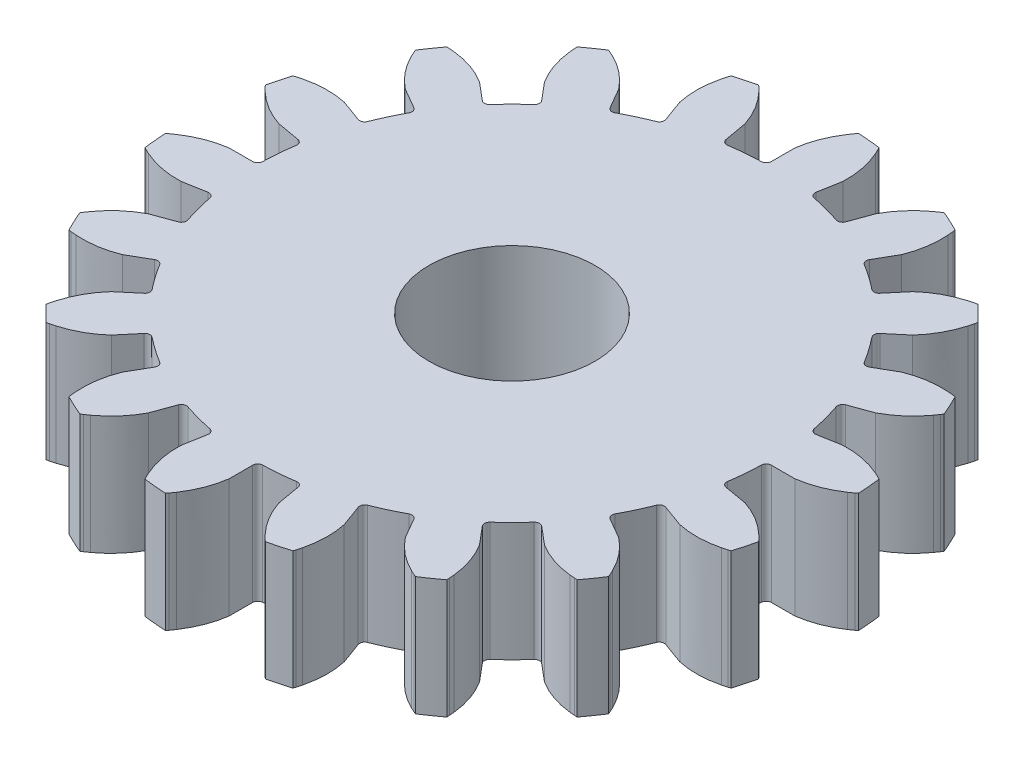
SolidWorks part; units mm, degrees
ref_plane "Front Plane" through (0, 0, 0) normal (0, 0, 1) x (1, 0, 0)
ref_plane "Top Plane" through (0, 0, 0) normal (0, 1, 0) x (1, 0, 0)
ref_plane "Right Plane" through (0, 0, 0) normal (1, 0, 0) x (0, 0, -1)
sketch "Sketch1" plane through (0, 0, 0) normal (0, 1, 0) x (1, 0, 0)
  line L0 (-10.9424, 9.3007) -> (-10.0385, 8.5423)
  line L1 (-8.5423, 10.0385) -> (-9.3007, 10.9424)
  line L2 (-7.1014, 12.4823) -> (-6.5115, 11.4605)
  line L3 (-2.4039, 14.1584) -> (-2.1991, 12.9964)
  line L4 (-0.0911, 13.1808) -> (-0.0911, 14.3607)
  line L5 (2.5835, 14.1267) -> (2.3786, 12.9647)
  line L6 (11.0595, 9.1611) -> (10.1557, 8.4026)
  line L7 (12.9964, -2.1991) -> (14.1584, -2.404)
  line L8 (13.4635, -4.9973) -> (12.3547, -4.5938)
  line L9 (4.5938, -12.3547) -> (4.9973, -13.4635)
  line L10 (-4.4225, -12.4171) -> (-4.826, -13.5258)
  line L11 (-8.4026, -10.1557) -> (-9.1611, -11.0595)
  line L12 (-12.9647, -2.3786) -> (-14.1267, -2.5835)
  line L13 (-14.3607, 0.0912) -> (-13.1808, 0.0912)
  line L14 (-12.9964, 2.1991) -> (-14.1584, 2.404)
  line L15 (-13.4635, 4.9973) -> (-12.3547, 4.5938)
  line L16 (-11.4605, 6.5115) -> (-12.4823, 7.1014)
  line L17 (2.4039, -14.1584) -> (2.1991, -12.9964)
  line L18 (-11.3693, -6.6693) -> (-12.3912, -7.2593)
  line L19 (8.4026, 10.1557) -> (9.1611, 11.0595)
  line L20 (-4.5938, 12.3547) -> (-4.9973, 13.4635)
  line L21 (-13.5258, -4.826) -> (-12.4171, -4.4224)
  line L22 (-2.5835, -14.1267) -> (-2.3786, -12.9647)
  line L23 (13.5258, 4.826) -> (12.4171, 4.4224)
  line L24 (-7.2593, -12.3912) -> (-6.6693, -11.3693)
  line L25 (12.9647, 2.3786) -> (14.1267, 2.5835)
  line L26 (14.3607, -0.0912) -> (13.1808, -0.0912)
  line L27 (-11.0595, -9.1611) -> (-10.1557, -8.4026)
  line L28 (7.2593, 12.3912) -> (6.6693, 11.3693)
  line L29 (8.5423, -10.0385) -> (9.3007, -10.9424)
  line L30 (10.9424, -9.3007) -> (10.0385, -8.5423)
  line L31 (11.4605, -6.5115) -> (12.4823, -7.1014)
  line L32 (11.3693, 6.6693) -> (12.3912, 7.2593)
  line L33 (7.1014, -12.4823) -> (6.5115, -11.4605)
  line L34 (4.4225, 12.4171) -> (4.826, 13.5258)
  line L35 (0.0911, -13.1808) -> (0.0911, -14.3607)
  circle A0 centre (0, 0) radius 4.191
  arc A2 (13.2871, -9.9977) -> (13.9392, -9.0664) centre (0, 0) ccw
  arc A4 (-15.3018, -6.5081) -> (-14.8213, -7.5385) centre (0, 0) ccw
  arc A6 (15.3018, 6.5081) -> (14.8213, 7.5385) centre (0, 0) ccw
  arc A8 (-13.2871, 9.9977) -> (-13.9392, 9.0664) centre (0, 0) ccw
  arc A10 (3.7521, -16.1994) -> (4.8503, -15.9052) centre (0, 0) ccw
  arc A12 (-9.0664, 13.9392) -> (-9.9977, 13.2871) centre (0, 0) ccw
  arc A14 (2.0147, 16.5058) -> (0.8821, 16.6049) centre (0, 0) ccw
  arc A16 (-2.0147, -16.5058) -> (-0.8821, -16.6049) centre (0, 0) ccw
  arc A19 (-15.9052, 4.8503) -> (-16.1994, 3.7521) centre (0, 0) ccw
  arc A20 (15.9052, -4.8503) -> (16.1994, -3.7521) centre (0, 0) ccw
  arc A22 (-16.6049, -0.8821) -> (-16.5058, -2.0147) centre (0, 0) ccw
  arc A24 (-7.5385, -14.8213) -> (-6.5081, -15.3018) centre (0, 0) ccw
  arc A26 (7.5385, 14.8213) -> (6.5081, 15.3018) centre (0, 0) ccw
  arc A28 (9.0664, -13.9392) -> (9.9977, -13.2871) centre (0, 0) ccw
  arc A30 (-3.7521, 16.1994) -> (-4.8503, 15.9052) centre (0, 0) ccw
  arc A32 (-12.153, -11.3492) -> (-11.3492, -12.153) centre (0, 0) ccw
  arc A34 (12.153, 11.3492) -> (11.3492, 12.153) centre (0, 0) ccw
  arc A36 (16.6049, 0.8821) -> (16.5058, 2.0147) centre (0, 0) ccw
  arc A38 (-10.0385, 8.5423) -> (-9.6782, 8.569) centre (-9.8721, 8.7406) ccw
  arc A39 (-8.569, 9.6782) -> (-9.6782, 8.569) centre (0, 0) ccw
  arc A40 (-8.569, 9.6782) -> (-8.5423, 10.0385) centre (-8.7406, 9.8721) ccw
  arc A41 (-6.5115, 11.4605) -> (-6.1638, 11.3624) centre (-6.2873, 11.5899) ccw
  arc A42 (-4.7421, 12.0253) -> (-6.1638, 11.3624) centre (0, 0) ccw
  arc A43 (-4.7421, 12.0253) -> (-4.5938, 12.3547) centre (-4.837, 12.2662) ccw
  arc A44 (-2.1991, 12.9964) -> (-1.9059, 12.7853) centre (-1.9441, 13.0413) ccw
  arc A45 (-0.3432, 12.922) -> (-1.9059, 12.7853) centre (0, 0) ccw
  arc A46 (-0.3432, 12.922) -> (-0.0911, 13.1808) centre (-0.35, 13.1808) ccw
  arc A47 (2.3786, 12.9647) -> (2.5818, 12.6661) centre (2.6336, 12.9198) ccw
  arc A48 (4.0971, 12.2601) -> (2.5818, 12.6661) centre (0, 0) ccw
  arc A49 (4.0971, 12.2601) -> (4.4225, 12.4171) centre (4.1792, 12.5056) ccw
  arc A50 (11.0192, 6.7582) -> (11.3693, 6.6693) centre (11.2399, 6.8935) ccw
  arc A51 (12.4171, 4.4224) -> (12.2601, 4.0971) centre (12.5056, 4.1792) ccw
  arc A52 (12.6661, 2.5818) -> (12.2601, 4.0971) centre (0, 0) ccw
  arc A53 (12.6661, 2.5818) -> (12.9647, 2.3786) centre (12.9198, 2.6335) ccw
  arc A54 (12.7853, -1.9059) -> (12.9964, -2.1991) centre (13.0413, -1.9441) ccw
  arc A55 (11.3624, -6.1638) -> (11.4605, -6.5115) centre (11.5899, -6.2873) ccw
  arc A56 (10.0385, -8.5423) -> (9.6782, -8.569) centre (9.8721, -8.7406) ccw
  arc A57 (8.569, -9.6782) -> (9.6782, -8.569) centre (0, 0) ccw
  arc A58 (8.569, -9.6782) -> (8.5423, -10.0385) centre (8.7406, -9.8721) ccw
  arc A59 (-8.0432, -10.1194) -> (-8.4026, -10.1557) centre (-8.2043, -10.3221) ccw
  arc A60 (-10.1557, -8.4026) -> (-10.1194, -8.0432) centre (-10.3221, -8.2043) ccw
  arc A61 (-12.7853, 1.9059) -> (-12.922, 0.3432) centre (0, 0) ccw
  arc A62 (-12.3547, 4.5938) -> (-12.0253, 4.7421) centre (-12.2662, 4.837) ccw
  arc A63 (-11.3624, 6.1638) -> (-12.0253, 4.7421) centre (0, 0) ccw
  arc A64 (-11.3624, 6.1638) -> (-11.4605, 6.5115) centre (-11.5899, 6.2873) ccw
  arc A65 (0.3432, -12.922) -> (0.0911, -13.1808) centre (0.35, -13.1808) ccw
  arc A66 (-2.3786, -12.9647) -> (-2.5818, -12.6661) centre (-2.6336, -12.9198) ccw
  arc A67 (-12.6661, -2.5818) -> (-12.9647, -2.3786) centre (-12.9198, -2.6335) ccw
  arc A68 (-4.0971, -12.2601) -> (-2.5818, -12.6661) centre (0, 0) ccw
  arc A69 (-4.0971, -12.2601) -> (-4.4225, -12.4171) centre (-4.1792, -12.5056) ccw
  arc A70 (-13.1808, 0.0912) -> (-12.922, 0.3432) centre (-13.1808, 0.35) ccw
  arc A71 (-6.6693, -11.3693) -> (-6.7582, -11.0192) centre (-6.8936, -11.2399) ccw
  arc A72 (0.3432, -12.922) -> (1.9059, -12.7853) centre (0, 0) ccw
  arc A73 (-8.0432, -10.1194) -> (-6.7582, -11.0192) centre (0, 0) ccw
  arc A74 (13.1808, -0.0912) -> (12.922, -0.3432) centre (13.1808, -0.35) ccw
  arc A75 (4.7421, -12.0253) -> (4.5938, -12.3547) centre (4.837, -12.2662) ccw
  arc A76 (-11.0192, -6.7582) -> (-10.1194, -8.0432) centre (0, 0) ccw
  arc A77 (-11.0192, -6.7582) -> (-11.3693, -6.6693) centre (-11.2399, -6.8935) ccw
  arc A78 (12.3547, -4.5938) -> (12.0253, -4.7421) centre (12.2662, -4.837) ccw
  arc A79 (-12.4171, -4.4224) -> (-12.2601, -4.0971) centre (-12.5056, -4.1792) ccw
  arc A80 (10.1557, 8.4026) -> (10.1194, 8.0432) centre (10.3221, 8.2043) ccw
  arc A81 (11.3624, -6.1638) -> (12.0253, -4.7421) centre (0, 0) ccw
  arc A82 (-12.6661, -2.5818) -> (-12.2601, -4.0971) centre (0, 0) ccw
  arc A83 (11.0192, 6.7582) -> (10.1194, 8.0432) centre (0, 0) ccw
  arc A84 (4.7421, -12.0253) -> (6.1638, -11.3624) centre (0, 0) ccw
  arc A85 (12.7853, -1.9059) -> (12.922, -0.3432) centre (0, 0) ccw
  arc A86 (-12.7853, 1.9059) -> (-12.9964, 2.1991) centre (-13.0413, 1.9441) ccw
  arc A87 (8.0432, 10.1194) -> (6.7582, 11.0192) centre (0, 0) ccw
  arc A88 (8.0432, 10.1194) -> (8.4026, 10.1557) centre (8.2043, 10.3221) ccw
  arc A89 (6.5115, -11.4605) -> (6.1638, -11.3624) centre (6.2873, -11.5899) ccw
  arc A90 (6.6693, 11.3693) -> (6.7582, 11.0192) centre (6.8936, 11.2399) ccw
  arc A91 (2.1991, -12.9964) -> (1.9059, -12.7853) centre (1.9441, -13.0413) ccw
  spline S0 degree 2 poles (13.2871, -9.9977) (13.2331, -9.9962) (13.1569, -9.9919) knots 0 0 0 0.5 0.5 0.5
  spline S1 degree 3 poles (13.1569, -9.9919) (13.0806, -9.9876) (12.9857, -9.9804) (12.8899, -9.97) knots 0.5 0.5 0.5 0.5 1 1 1 1
  spline S2 degree 3 poles (13.7773, -8.7026) (13.8199, -8.7893) (13.8591, -8.8757) (13.889, -8.9455) knots 0 0 0 0 0.5 0.5 0.5 0.5
  spline S3 degree 2 poles (13.889, -8.9455) (13.919, -9.0153) (13.9392, -9.0664) knots 0.5 0.5 0.5 1 1 1
  spline S4 degree 2 poles (-15.3018, -6.5081) (-15.2735, -6.4621) (-15.2317, -6.3982) knots 0 0 0 0.5 0.5 0.5
  spline S5 degree 3 poles (-15.2317, -6.3982) (-15.1898, -6.3343) (-15.1361, -6.2558) (-15.0792, -6.178) knots 0.5 0.5 0.5 0.5 1 1 1 1
  spline S6 degree 3 poles (-14.4254, -7.5802) (-14.5217, -7.5738) (-14.6161, -7.5645) (-14.6915, -7.5555) knots 0 0 0 0 0.5 0.5 0.5 0.5
  spline S7 degree 2 poles (-14.6915, -7.5555) (-14.7669, -7.5466) (-14.8213, -7.5385) knots 0.5 0.5 0.5 1 1 1
  spline S8 degree 2 poles (15.3018, 6.5081) (15.2735, 6.4621) (15.2317, 6.3982) knots 0 0 0 0.5 0.5 0.5
  spline S9 degree 3 poles (15.2317, 6.3982) (15.1898, 6.3343) (15.1361, 6.2558) (15.0792, 6.178) knots 0.5 0.5 0.5 0.5 1 1 1 1
  spline S10 degree 3 poles (14.4254, 7.5802) (14.5217, 7.5738) (14.6161, 7.5645) (14.6915, 7.5555) knots 0 0 0 0 0.5 0.5 0.5 0.5
  spline S11 degree 2 poles (14.6915, 7.5555) (14.7669, 7.5466) (14.8213, 7.5385) knots 0.5 0.5 0.5 1 1 1
  spline S12 degree 2 poles (-13.2871, 9.9977) (-13.2331, 9.9962) (-13.1569, 9.9919) knots 0 0 0 0.5 0.5 0.5
  spline S13 degree 3 poles (-13.1569, 9.9919) (-13.0806, 9.9876) (-12.9857, 9.9804) (-12.8899, 9.97) knots 0.5 0.5 0.5 0.5 1 1 1 1
  spline S14 degree 3 poles (-13.7773, 8.7026) (-13.8199, 8.7893) (-13.8591, 8.8757) (-13.889, 8.9455) knots 0 0 0 0 0.5 0.5 0.5 0.5
  spline S15 degree 2 poles (-13.889, 8.9455) (-13.919, 9.0153) (-13.9392, 9.0664) knots 0.5 0.5 0.5 1 1 1
  spline S16 degree 2 poles (3.7521, -16.1994) (3.7117, -16.1636) (3.6561, -16.1113) knots 0 0 0 0.5 0.5 0.5
  spline S17 degree 3 poles (3.6561, -16.1113) (3.6004, -16.059) (3.5324, -15.9925) (3.4657, -15.9229) knots 0.5 0.5 0.5 0.5 1 1 1 1
  spline S18 degree 3 poles (4.9601, -15.5225) (4.9371, -15.6162) (4.9115, -15.7076) (4.8896, -15.7803) knots 0 0 0 0 0.5 0.5 0.5 0.5
  spline S19 degree 2 poles (4.8896, -15.7803) (4.8677, -15.853) (4.8503, -15.9052) knots 0.5 0.5 0.5 1 1 1
  spline S20 degree 2 poles (-9.0664, 13.9392) (-9.0162, 13.9194) (-8.946, 13.8892) knots 0 0 0 0.5 0.5 0.5
  spline S21 degree 3 poles (-8.946, 13.8892) (-8.8758, 13.8591) (-8.7891, 13.8199) (-8.7026, 13.7773) knots 0.5 0.5 0.5 0.5 1 1 1 1
  spline S22 degree 3 poles (-9.97, 12.8899) (-9.9804, 12.9859) (-9.9876, 13.0805) (-9.9919, 13.1563) knots 0 0 0 0 0.5 0.5 0.5 0.5
  spline S23 degree 2 poles (-9.9919, 13.1563) (-9.9962, 13.2321) (-9.9977, 13.2871) knots 0.5 0.5 0.5 1 1 1
  spline S24 degree 2 poles (2.0147, 16.5058) (2.0404, 16.4583) (2.0748, 16.3901) knots 0 0 0 0.5 0.5 0.5
  spline S25 degree 3 poles (2.0748, 16.3901) (2.1092, 16.3219) (2.1504, 16.2362) (2.1893, 16.148) knots 0.5 0.5 0.5 0.5 1 1 1 1
  spline S26 degree 3 poles (0.648, 16.2828) (0.7017, 16.3631) (0.7571, 16.4402) (0.8025, 16.501) knots 0 0 0 0 0.5 0.5 0.5 0.5
  spline S27 degree 2 poles (0.8025, 16.501) (0.848, 16.5618) (0.8821, 16.6049) knots 0.5 0.5 0.5 1 1 1
  spline S28 degree 2 poles (-2.0147, -16.5058) (-2.0404, -16.4583) (-2.0748, -16.3901) knots 0 0 0 0.5 0.5 0.5
  spline S29 degree 3 poles (-2.0748, -16.3901) (-2.1092, -16.3219) (-2.1504, -16.2362) (-2.1893, -16.148) knots 0.5 0.5 0.5 0.5 1 1 1 1
  spline S30 degree 3 poles (-0.648, -16.2828) (-0.7017, -16.3631) (-0.7571, -16.4402) (-0.8025, -16.501) knots 0 0 0 0 0.5 0.5 0.5 0.5
  spline S31 degree 2 poles (-0.8025, -16.501) (-0.848, -16.5618) (-0.8821, -16.6049) knots 0.5 0.5 0.5 1 1 1
  spline S32 degree 3 poles (-15.9229, 3.4657) (-15.9926, 3.5325) (-16.059, 3.6004) (-16.111, 3.6557) knots 0 0 0 0 0.5 0.5 0.5 0.5
  spline S33 degree 2 poles (-16.111, 3.6557) (-16.163, 3.711) (-16.1994, 3.7521) knots 0.5 0.5 0.5 1 1 1
  spline S34 degree 2 poles (-15.9052, 4.8503) (-15.854, 4.8674) (-15.7808, 4.8894) knots 0 0 0 0.5 0.5 0.5
  spline S35 degree 3 poles (-15.7808, 4.8894) (-15.7077, 4.9115) (-15.6161, 4.9371) (-15.5225, 4.9601) knots 0.5 0.5 0.5 0.5 1 1 1 1
  spline S36 degree 2 poles (15.9052, -4.8503) (15.854, -4.8674) (15.7808, -4.8894) knots 0 0 0 0.5 0.5 0.5
  spline S37 degree 3 poles (15.7808, -4.8894) (15.7077, -4.9115) (15.6161, -4.9371) (15.5225, -4.9601) knots 0.5 0.5 0.5 0.5 1 1 1 1
  spline S38 degree 3 poles (15.9229, -3.4657) (15.9926, -3.5325) (16.059, -3.6004) (16.111, -3.6557) knots 0 0 0 0 0.5 0.5 0.5 0.5
  spline S39 degree 2 poles (16.111, -3.6557) (16.163, -3.711) (16.1994, -3.7521) knots 0.5 0.5 0.5 1 1 1
  spline S40 degree 2 poles (-16.6049, -0.8821) (-16.5626, -0.8486) (-16.5014, -0.8028) knots 0 0 0 0.5 0.5 0.5
  spline S41 degree 3 poles (-16.5014, -0.8028) (-16.4402, -0.7571) (-16.3629, -0.7016) (-16.2828, -0.648) knots 0.5 0.5 0.5 0.5 1 1 1 1
  spline S42 degree 3 poles (-16.148, -2.1893) (-16.2363, -2.1503) (-16.3219, -2.1093) (-16.3897, -2.0751) knots 0 0 0 0 0.5 0.5 0.5 0.5
  spline S43 degree 2 poles (-16.3897, -2.0751) (-16.4574, -2.0409) (-16.5058, -2.0147) knots 0.5 0.5 0.5 1 1 1
  spline S44 degree 2 poles (-7.5385, -14.8213) (-7.5464, -14.7679) (-7.5554, -14.6921) knots 0 0 0 0.5 0.5 0.5
  spline S45 degree 3 poles (-7.5554, -14.6921) (-7.5645, -14.6162) (-7.5738, -14.5215) (-7.5802, -14.4254) knots 0.5 0.5 0.5 0.5 1 1 1 1
  spline S46 degree 3 poles (-6.178, -15.0792) (-6.2559, -15.1362) (-6.3343, -15.1898) (-6.3978, -15.2314) knots 0 0 0 0 0.5 0.5 0.5 0.5
  spline S47 degree 2 poles (-6.3978, -15.2314) (-6.4613, -15.273) (-6.5081, -15.3018) knots 0.5 0.5 0.5 1 1 1
  spline S48 degree 2 poles (7.5385, 14.8213) (7.5464, 14.7679) (7.5554, 14.6921) knots 0 0 0 0.5 0.5 0.5
  spline S49 degree 3 poles (7.5554, 14.6921) (7.5645, 14.6162) (7.5738, 14.5215) (7.5802, 14.4254) knots 0.5 0.5 0.5 0.5 1 1 1 1
  spline S50 degree 3 poles (6.178, 15.0792) (6.2559, 15.1362) (6.3343, 15.1898) (6.3978, 15.2314) knots 0 0 0 0 0.5 0.5 0.5 0.5
  spline S51 degree 2 poles (6.3978, 15.2314) (6.4613, 15.273) (6.5081, 15.3018) knots 0.5 0.5 0.5 1 1 1
  spline S52 degree 2 poles (9.0664, -13.9392) (9.0162, -13.9194) (8.946, -13.8892) knots 0 0 0 0.5 0.5 0.5
  spline S53 degree 3 poles (8.946, -13.8892) (8.8758, -13.8591) (8.7891, -13.8199) (8.7026, -13.7773) knots 0.5 0.5 0.5 0.5 1 1 1 1
  spline S54 degree 3 poles (9.97, -12.8899) (9.9804, -12.9859) (9.9876, -13.0805) (9.9919, -13.1563) knots 0 0 0 0 0.5 0.5 0.5 0.5
  spline S55 degree 2 poles (9.9919, -13.1563) (9.9962, -13.2321) (9.9977, -13.2871) knots 0.5 0.5 0.5 1 1 1
  spline S56 degree 2 poles (-3.7521, 16.1994) (-3.7117, 16.1636) (-3.6561, 16.1113) knots 0 0 0 0.5 0.5 0.5
  spline S57 degree 3 poles (-3.6561, 16.1113) (-3.6004, 16.059) (-3.5324, 15.9925) (-3.4657, 15.9229) knots 0.5 0.5 0.5 0.5 1 1 1 1
  spline S58 degree 3 poles (-4.9601, 15.5225) (-4.9371, 15.6162) (-4.9115, 15.7076) (-4.8896, 15.7803) knots 0 0 0 0 0.5 0.5 0.5 0.5
  spline S59 degree 2 poles (-4.8896, 15.7803) (-4.8677, 15.853) (-4.8503, 15.9052) knots 0.5 0.5 0.5 1 1 1
  spline S60 degree 2 poles (-12.153, -11.3492) (-12.1423, -11.2963) (-12.1248, -11.2219) knots 0 0 0 0.5 0.5 0.5
  spline S61 degree 3 poles (-12.1248, -11.2219) (-12.1073, -11.1475) (-12.0837, -11.0554) (-12.0568, -10.9628) knots 0.5 0.5 0.5 0.5 1 1 1 1
  spline S62 degree 3 poles (-10.9628, -12.0568) (-11.0555, -12.0838) (-11.1475, -12.1073) (-11.2214, -12.1247) knots 0 0 0 0 0.5 0.5 0.5 0.5
  spline S63 degree 2 poles (-11.2214, -12.1247) (-11.2953, -12.142) (-11.3492, -12.153) knots 0.5 0.5 0.5 1 1 1
  spline S64 degree 2 poles (12.153, 11.3492) (12.1423, 11.2963) (12.1248, 11.2219) knots 0 0 0 0.5 0.5 0.5
  spline S65 degree 3 poles (12.1248, 11.2219) (12.1073, 11.1475) (12.0837, 11.0554) (12.0568, 10.9628) knots 0.5 0.5 0.5 0.5 1 1 1 1
  spline S66 degree 3 poles (10.9628, 12.0568) (11.0555, 12.0838) (11.1475, 12.1073) (11.2214, 12.1247) knots 0 0 0 0 0.5 0.5 0.5 0.5
  spline S67 degree 2 poles (11.2214, 12.1247) (11.2953, 12.142) (11.3492, 12.153) knots 0.5 0.5 0.5 1 1 1
  spline S68 degree 2 poles (16.6049, 0.8821) (16.5626, 0.8486) (16.5014, 0.8028) knots 0 0 0 0.5 0.5 0.5
  spline S69 degree 3 poles (16.5014, 0.8028) (16.4402, 0.7571) (16.3629, 0.7016) (16.2828, 0.648) knots 0.5 0.5 0.5 0.5 1 1 1 1
  spline S70 degree 3 poles (16.148, 2.1893) (16.2363, 2.1503) (16.3219, 2.1093) (16.3897, 2.0751) knots 0 0 0 0 0.5 0.5 0.5 0.5
  spline S71 degree 2 poles (16.3897, 2.0751) (16.4574, 2.0409) (16.5058, 2.0147) knots 0.5 0.5 0.5 1 1 1
  spline S72 degree 3 poles (-8.7026, 13.7773) (-8.0617, 13.4621) (-7.5279, 13.0304) (-7.1014, 12.4823) knots 0.176125 0.176125 0.176125 0.176125 1 1 1 1
  spline S73 degree 3 poles (-15.0792, -6.178) (-14.6574, -5.6015) (-14.1396, -5.1509) (-13.5258, -4.826) knots 0.176125 0.176125 0.176125 0.176125 1 1 1 1
  spline S74 degree 3 poles (-2.1893, -16.148) (-2.4776, -15.4945) (-2.609, -14.8207) (-2.5835, -14.1267) knots 0.176125 0.176125 0.176125 0.176125 1 1 1 1
  spline S75 degree 3 poles (15.0792, 6.178) (14.6574, 5.6015) (14.1396, 5.1509) (13.5258, 4.826) knots 0.176125 0.176125 0.176125 0.176125 1 1 1 1
  spline S76 degree 3 poles (7.5802, 14.4254) (7.6276, 13.7126) (7.5207, 13.0346) (7.2593, 12.3912) knots 0.176125 0.176125 0.176125 0.176125 1 1 1 1
  spline S77 degree 3 poles (2.1893, 16.148) (2.4776, 15.4945) (2.609, 14.8207) (2.5835, 14.1267) knots 0.176125 0.176125 0.176125 0.176125 1 1 1 1
  spline S78 degree 3 poles (-16.2828, -0.648) (-15.6893, -0.2506) (-15.0486, -0.0042) (-14.3607, 0.0912) knots 0.176125 0.176125 0.176125 0.176125 1 1 1 1
  spline S79 degree 3 poles (16.2828, 0.648) (15.6893, 0.2506) (15.0486, 0.0042) (14.3607, -0.0912) knots 0.176125 0.176125 0.176125 0.176125 1 1 1 1
  spline S80 degree 3 poles (12.8899, -9.97) (12.1798, -9.8929) (11.5306, -9.6698) (10.9424, -9.3007) knots 0.176125 0.176125 0.176125 0.176125 1 1 1 1
  spline S81 degree 3 poles (12.0568, 10.9628) (11.8576, 10.2769) (11.5252, 9.6763) (11.0595, 9.1611) knots 0.176125 0.176125 0.176125 0.176125 1 1 1 1
  spline S82 degree 3 poles (-12.8899, 9.97) (-12.1798, 9.8929) (-11.5306, 9.6698) (-10.9424, 9.3007) knots 0.176125 0.176125 0.176125 0.176125 1 1 1 1
  spline S83 degree 3 poles (8.7026, -13.7773) (8.0617, -13.4621) (7.5279, -13.0304) (7.1014, -12.4823) knots 0.176125 0.176125 0.176125 0.176125 1 1 1 1
  spline S84 degree 3 poles (3.4657, -15.9229) (2.9712, -15.4074) (2.6173, -14.8193) (2.4039, -14.1584) knots 0.176125 0.176125 0.176125 0.176125 1 1 1 1
  spline S85 degree 3 poles (-7.5802, -14.4254) (-7.6276, -13.7126) (-7.5207, -13.0346) (-7.2593, -12.3912) knots 0.176125 0.176125 0.176125 0.176125 1 1 1 1
  spline S86 degree 3 poles (-12.0568, -10.9628) (-11.8576, -10.2769) (-11.5252, -9.6763) (-11.0595, -9.1611) knots 0.176125 0.176125 0.176125 0.176125 1 1 1 1
  spline S87 degree 3 poles (-3.4657, 15.9229) (-2.9712, 15.4074) (-2.6173, 14.8193) (-2.4039, 14.1584) knots 0.176125 0.176125 0.176125 0.176125 1 1 1 1
  spline S88 degree 3 poles (-15.5225, 4.9601) (-14.8288, 5.1306) (-14.1425, 5.143) (-13.4635, 4.9973) knots 0.176125 0.176125 0.176125 0.176125 1 1 1 1
  spline S89 degree 3 poles (15.5225, -4.9601) (14.8288, -5.1306) (14.1425, -5.143) (13.4635, -4.9973) knots 0.176125 0.176125 0.176125 0.176125 1 1 1 1
  spline S90 degree 3 poles (14.1267, 2.5835) (14.8207, 2.609) (15.4945, 2.4776) (16.148, 2.1893) knots 0 0 0 0 0.823875 0.823875 0.823875 0.823875
  spline S91 degree 3 poles (9.1611, 11.0595) (9.6763, 11.5252) (10.2769, 11.8576) (10.9628, 12.0568) knots 0 0 0 0 0.823875 0.823875 0.823875 0.823875
  spline S92 degree 3 poles (-9.1611, -11.0595) (-9.6763, -11.5252) (-10.2769, -11.8576) (-10.9628, -12.0568) knots 0 0 0 0 0.823875 0.823875 0.823875 0.823875
  spline S93 degree 3 poles (-4.9973, 13.4635) (-5.143, 14.1425) (-5.1306, 14.8288) (-4.9601, 15.5225) knots 0 0 0 0 0.823875 0.823875 0.823875 0.823875
  spline S94 degree 3 poles (9.3007, -10.9424) (9.6698, -11.5306) (9.8929, -12.1798) (9.97, -12.8899) knots 0 0 0 0 0.823875 0.823875 0.823875 0.823875
  spline S95 degree 3 poles (4.826, 13.5258) (5.1509, 14.1396) (5.6015, 14.6574) (6.178, 15.0792) knots 0 0 0 0 0.823875 0.823875 0.823875 0.823875
  spline S96 degree 3 poles (-4.826, -13.5258) (-5.1509, -14.1396) (-5.6015, -14.6574) (-6.178, -15.0792) knots 0 0 0 0 0.823875 0.823875 0.823875 0.823875
  spline S97 degree 3 poles (-14.1267, -2.5835) (-14.8207, -2.609) (-15.4945, -2.4776) (-16.148, -2.1893) knots 0 0 0 0 0.823875 0.823875 0.823875 0.823875
  spline S98 degree 3 poles (-14.1584, 2.404) (-14.8193, 2.6173) (-15.4074, 2.9712) (-15.9229, 3.4657) knots 0 0 0 0 0.823875 0.823875 0.823875 0.823875
  spline S99 degree 3 poles (14.1584, -2.404) (14.8193, -2.6173) (15.4074, -2.9712) (15.9229, -3.4657) knots 0 0 0 0 0.823875 0.823875 0.823875 0.823875
  spline S100 degree 3 poles (0.0911, -14.3607) (-0.0042, -15.0486) (-0.2506, -15.6893) (-0.648, -16.2828) knots 0 0 0 0 0.823875 0.823875 0.823875 0.823875
  spline S101 degree 3 poles (-0.0911, 14.3607) (0.0042, 15.0486) (0.2506, 15.6893) (0.648, 16.2828) knots 0 0 0 0 0.823875 0.823875 0.823875 0.823875
  spline S102 degree 3 poles (-9.3007, 10.9424) (-9.6698, 11.5306) (-9.8929, 12.1798) (-9.97, 12.8899) knots 0 0 0 0 0.823875 0.823875 0.823875 0.823875
  spline S103 degree 3 poles (4.9973, -13.4635) (5.143, -14.1425) (5.1306, -14.8288) (4.9601, -15.5225) knots 0 0 0 0 0.823875 0.823875 0.823875 0.823875
  spline S104 degree 3 poles (-12.4823, 7.1014) (-13.0304, 7.5279) (-13.462, 8.0617) (-13.7773, 8.7026) knots 0 0 0 0 0.823875 0.823875 0.823875 0.823875
  spline S105 degree 3 poles (12.3912, 7.2593) (13.0346, 7.5207) (13.7126, 7.6276) (14.4254, 7.5802) knots 0 0 0 0 0.823875 0.823875 0.823875 0.823875
  spline S106 degree 3 poles (-12.3912, -7.2593) (-13.0346, -7.5207) (-13.7126, -7.6276) (-14.4254, -7.5802) knots 0 0 0 0 0.823875 0.823875 0.823875 0.823875
  spline S107 degree 3 poles (12.4823, -7.1014) (13.0304, -7.5279) (13.462, -8.0617) (13.7773, -8.7026) knots 0 0 0 0 0.823875 0.823875 0.823875 0.823875
  dimension "D1" = 8.382
extrude "Boss-Extrude1" add sketch "Sketch1" along normal blind 6
